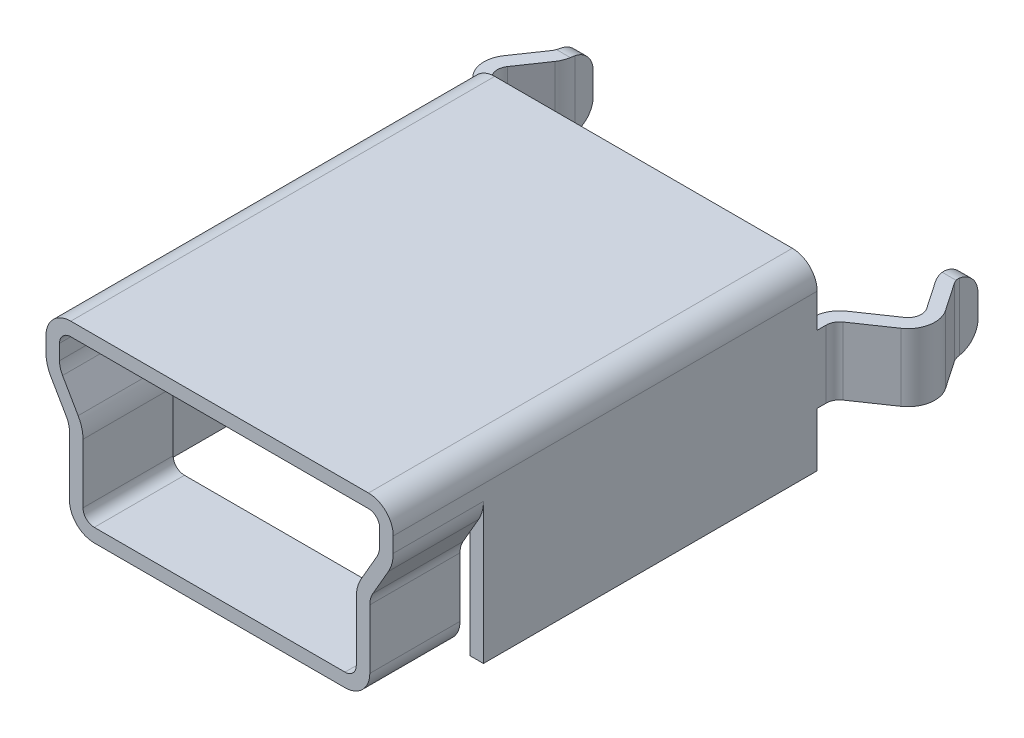
SolidWorks part; units mm, degrees
material "AISI 304"
ref_plane "Front" through (0, 0, 0) normal (0, 0, 1) x (1, 0, 0)
ref_plane "Top" through (0, 0, 0) normal (0, 1, 0) x (1, 0, 0)
ref_plane "Right" through (0, 0, 0) normal (1, 0, 0) x (0, 0, -1)
sketch "Sketch1" plane through (0, 0, 0) normal (0, 0, 1) x (1, 0, 0)
  line L0 (-9.6683, 0) -> (6.8815, 0) construction
  line L1 (0, 0) -> (0, 11.7001) construction
  line L2 (-5.9083, 0) -> (2.78, 0)
  line L3 (3.33, 0.55) -> (3.33, 1.866)
  line L4 (3.397, 2.116) -> (3.7428, 2.715)
  line L5 (3.85, 3.115) -> (3.85, 3.45)
  line L6 (3.3, 4) -> (-13.106, 4)
  line L7 (-4.35, 0.3) -> (2.78, 0.3)
  line L8 (3.03, 0.55) -> (3.03, 1.866)
  line L9 (3.1372, 2.266) -> (3.483, 2.865)
  line L10 (3.55, 3.115) -> (3.55, 3.45)
  line L11 (3.3, 3.7) -> (-10.3781, 3.7)
  line L12 (1.5, 2.2) -> (1.5, 1.64)
  line L13 (-2.3, 2.75) -> (2.3, 2.75)
  line L14 (-2.3, 2.75) -> (-2.3, 1.85)
  line L15 (-1.55, 1.1) -> (1.55, 1.1)
  line L16 (2.3, 2.75) -> (2.3, 1.85)
  line L17 (-1.8, 2.2) -> (-1.5, 2.2)
  line L18 (-1.8, 2.2) -> (-1.8, 1.64)
  line L19 (-1.8, 1.64) -> (-1.5, 1.64)
  line L20 (1.8, 2.2) -> (1.8, 1.64)
  line L21 (0.98, 2.2) -> (0.98, 1.64)
  line L22 (0.68, 2.2) -> (0.68, 1.64)
  line L23 (0.15, 2.2) -> (0.15, 1.64)
  line L24 (1.5, 2.2) -> (1.8, 2.2)
  line L25 (1.5, 1.64) -> (1.8, 1.64)
  line L26 (0.68, 2.2) -> (0.98, 2.2)
  line L27 (0.68, 1.64) -> (0.98, 1.64)
  line L28 (-0.15, 2.2) -> (-0.15, 1.64)
  line L29 (-1.5, 2.2) -> (-1.5, 1.64)
  line L30 (-0.98, 2.2) -> (-0.98, 1.64)
  line L31 (-0.68, 2.2) -> (-0.68, 1.64)
  line L32 (-0.15, 1.64) -> (0.15, 1.64)
  line L33 (-0.15, 2.2) -> (0.15, 2.2)
  line L34 (-0.98, 2.2) -> (-0.68, 2.2)
  line L35 (-0.98, 1.64) -> (-0.68, 1.64)
  arc A0 (-2.3, 1.85) -> (-1.55, 1.1) centre (-1.55, 1.85) ccw
  arc A1 (1.55, 1.1) -> (2.3, 1.85) centre (1.55, 1.85) ccw
  arc A2 (3.483, 2.865) -> (3.55, 3.115) centre (3.05, 3.115) ccw
  arc A3 (3.33, 1.866) -> (3.397, 2.116) centre (3.83, 1.866) cw
  arc A4 (3.7428, 2.715) -> (3.85, 3.115) centre (3.05, 3.115) ccw
  arc A5 (3.03, 1.866) -> (3.1372, 2.266) centre (3.83, 1.866) cw
  arc A6 (3.55, 3.45) -> (3.3, 3.7) centre (3.3, 3.45) ccw
  arc A7 (3.85, 3.45) -> (3.3, 4) centre (3.3, 3.45) ccw
  arc A8 (2.78, 0) -> (3.33, 0.55) centre (2.78, 0.55) ccw
  arc A9 (2.78, 0.3) -> (3.03, 0.55) centre (2.78, 0.55) ccw
  point P49 (3.33, 2)
  point P60 (3.33, 0)
  dimension "D14" = 0.75
  dimension "D22" = 0.5
  dimension "D23" = 0.8
  dimension "D24" = 0.25
  dimension "D25" = 0.55
  dimension "D1" = 0.3
  dimension "D2" = 0.3
  dimension "D3" = 0.3
  dimension "D4" = 0.3
  dimension "D5" = 0.3
  dimension "D6" = 4
  dimension "D7" = 6.66
  dimension "D8" = 60
  dimension "D9" = 7.7
  dimension "D10" = 2
  dimension "D11" = 1.1
  dimension "D12" = 2.75
  dimension "D13" = 4.6
  dimension "D15" = 2.2
  dimension "D16" = 1.64
  dimension "D17" = 3.6
  dimension "D18" = 0.3
  dimension "D19" = 0.82
  dimension "D20" = 0.53
  dimension "D21" = 0.52
sketch "Sketch2" plane through (0, 0, 0) normal (0, 0, 1) x (1, 0, 0)
  line L0 (-5.9083, 0) -> (2.78, 0) construction
  line L1 (3.33, 0.55) -> (3.33, 1.866) construction
  line L2 (3.397, 2.116) -> (3.7428, 2.715) construction
  line L3 (3.85, 3.115) -> (3.85, 3.45) construction
  line L4 (3.3, 4) -> (-13.106, 4) construction
  line L5 (0, 0) -> (2.78, 0)
  line L6 (3.33, 0.55) -> (3.33, 1.866)
  line L7 (3.397, 2.116) -> (3.7428, 2.715)
  line L8 (3.85, 3.115) -> (3.85, 3.45)
  line L9 (3.3, 4) -> (0, 4)
  line L10 (-4.35, 0.3) -> (2.78, 0.3) construction
  line L11 (3.03, 0.55) -> (3.03, 1.866) construction
  line L12 (3.1372, 2.266) -> (3.483, 2.865) construction
  line L13 (3.55, 3.115) -> (3.55, 3.45) construction
  line L14 (3.3, 3.7) -> (-10.3781, 3.7) construction
  line L15 (0, 0.3) -> (2.78, 0.3)
  line L16 (3.03, 0.55) -> (3.03, 1.866)
  line L17 (3.1372, 2.266) -> (3.483, 2.865)
  line L18 (3.55, 3.115) -> (3.55, 3.45)
  line L19 (3.3, 3.7) -> (0, 3.7)
  line L20 (0, 4) -> (0, 3.7)
  line L22 (0, 0.3) -> (0, 0)
  arc A0 (2.78, 0) -> (3.33, 0.55) centre (2.78, 0.55) ccw construction
  arc A1 (3.397, 2.116) -> (3.33, 1.866) centre (3.83, 1.866) ccw construction
  arc A2 (3.7428, 2.715) -> (3.85, 3.115) centre (3.05, 3.115) ccw construction
  arc A3 (3.85, 3.45) -> (3.3, 4) centre (3.3, 3.45) ccw construction
  arc A4 (2.78, 0) -> (3.33, 0.55) centre (2.78, 0.55) ccw
  arc A5 (3.397, 2.116) -> (3.33, 1.866) centre (3.83, 1.866) ccw
  arc A6 (3.7428, 2.715) -> (3.85, 3.115) centre (3.05, 3.115) ccw
  arc A7 (3.85, 3.45) -> (3.3, 4) centre (3.3, 3.45) ccw
  arc A8 (2.78, 0.3) -> (3.03, 0.55) centre (2.78, 0.55) ccw construction
  arc A9 (3.1372, 2.266) -> (3.03, 1.866) centre (3.83, 1.866) ccw construction
  arc A10 (3.483, 2.865) -> (3.55, 3.115) centre (3.05, 3.115) ccw construction
  arc A11 (3.55, 3.45) -> (3.3, 3.7) centre (3.3, 3.45) ccw construction
  arc A12 (2.78, 0.3) -> (3.03, 0.55) centre (2.78, 0.55) ccw
  arc A13 (3.1372, 2.266) -> (3.03, 1.866) centre (3.83, 1.866) ccw
  arc A14 (3.483, 2.865) -> (3.55, 3.115) centre (3.05, 3.115) ccw
  arc A15 (3.55, 3.45) -> (3.3, 3.7) centre (3.3, 3.45) ccw
extrude "Boss-Extrude1" add sketch "Sketch2" against normal blind 2
sketch "Sketch4" plane through (0, 0, -2) normal (0, 0, -1) x (-1, 0, 0)
  line L0 (9.6683, 0) -> (-6.8815, 0) construction
  line L1 (-3.85, 3.115) -> (-3.85, 3.45) construction
  line L2 (-3.55, 3.115) -> (-3.55, 3.45) construction
  line L3 (-3.3, 3.7) -> (10.3781, 3.7) construction
  line L4 (-3.3, 4) -> (13.106, 4) construction
  line L5 (0, 0) -> (0, 11.7001) construction
  line L6 (-3.55, 0) -> (-3.85, 0)
  line L7 (-3.85, 0) -> (-3.85, 3.45)
  line L8 (-3.55, 0) -> (-3.55, 3.45)
  line L9 (-3.3, 3.7) -> (0, 3.7)
  line L10 (-3.3, 4) -> (0, 4)
  line L11 (0, 3.7) -> (0, 4)
  arc A0 (-3.3, 4) -> (-3.85, 3.45) centre (-3.3, 3.45) ccw construction
  arc A1 (-3.3, 3.7) -> (-3.55, 3.45) centre (-3.3, 3.45) ccw construction
  arc A2 (-3.3, 4) -> (-3.85, 3.45) centre (-3.3, 3.45) ccw
  arc A3 (-3.3, 3.7) -> (-3.55, 3.45) centre (-3.3, 3.45) ccw
extrude "Boss-Extrude2" add sketch "Sketch4" along normal blind 7.4
ref_plane "Plane1" through (0, 1.2, 0) normal (0, 1, 0) x (1, 0, 0)
sketch "Sketch5" plane through (0, 1.2, 0) normal (0, 1, 0) x (1, 0, 0)
  line L0 (3.85, 9.4) -> (3.55, 9.4) construction
  line L1 (3.85, 9.4) -> (3.55, 9.4)
  line L2 (3.9806, 9.8476) -> (4.7387, 10.3661)
  line L3 (4.8953, 11.2) -> (4.4689, 11.8234)
  line L4 (4.4165, 11.9928) -> (4.4165, 12.4)
  line L5 (4.4165, 12.4) -> (4.1165, 12.4)
  line L6 (4.1165, 12.4) -> (4.1165, 11.9928)
  line L7 (4.2213, 11.6541) -> (4.6476, 11.0307)
  line L8 (4.5694, 10.6137) -> (3.8113, 10.0953)
  line L9 (3.55, 9.4) -> (3.55, 2) construction
  line L10 (3.85, 9.4) -> (3.85, 2) construction
  line L11 (3.55, 9.6) -> (3.55, 9.4)
  line L12 (3.85, 9.6) -> (3.85, 9.4)
  line L13 (0, 0) -> (0, 13.4866) construction
  arc A0 (4.4689, 11.8234) -> (4.4165, 11.9928) centre (4.7165, 11.9928) cw
  arc A1 (4.6476, 11.0307) -> (4.5694, 10.6137) centre (4.4, 10.8613) cw
  arc A2 (3.9806, 9.8476) -> (3.85, 9.6) centre (4.15, 9.6) ccw
  arc A3 (3.8113, 10.0953) -> (3.55, 9.6) centre (4.15, 9.6) ccw
  arc A4 (4.7387, 10.3661) -> (4.8953, 11.2) centre (4.4, 10.8613) ccw
  arc A5 (4.1165, 11.9928) -> (4.2213, 11.6541) centre (4.7165, 11.9928) ccw
  point P17 (4.4165, 11.9)
  dimension "D6" = 0.3
  dimension "D7" = 0.6
  dimension "D8" = 10
  dimension "D1" = 0.3
  dimension "D2" = 0.3
  dimension "D3" = 0.3
  dimension "D4" = 3
  dimension "D5" = 0.5
  dimension "D9" = 0.2
  dimension "D10" = 8.8331
extrude "Boss-Extrude3" add sketch "Sketch5" along normal blind 1.5
fillet "Fillet1" radius 0.5 2 edges at (4.2665, 1.2, -12.4) (4.2665, 2.7, -12.4)
mirror "Mirror1" about plane through (0, 4, -2) normal (-1, 0, 0) of bodies 103
